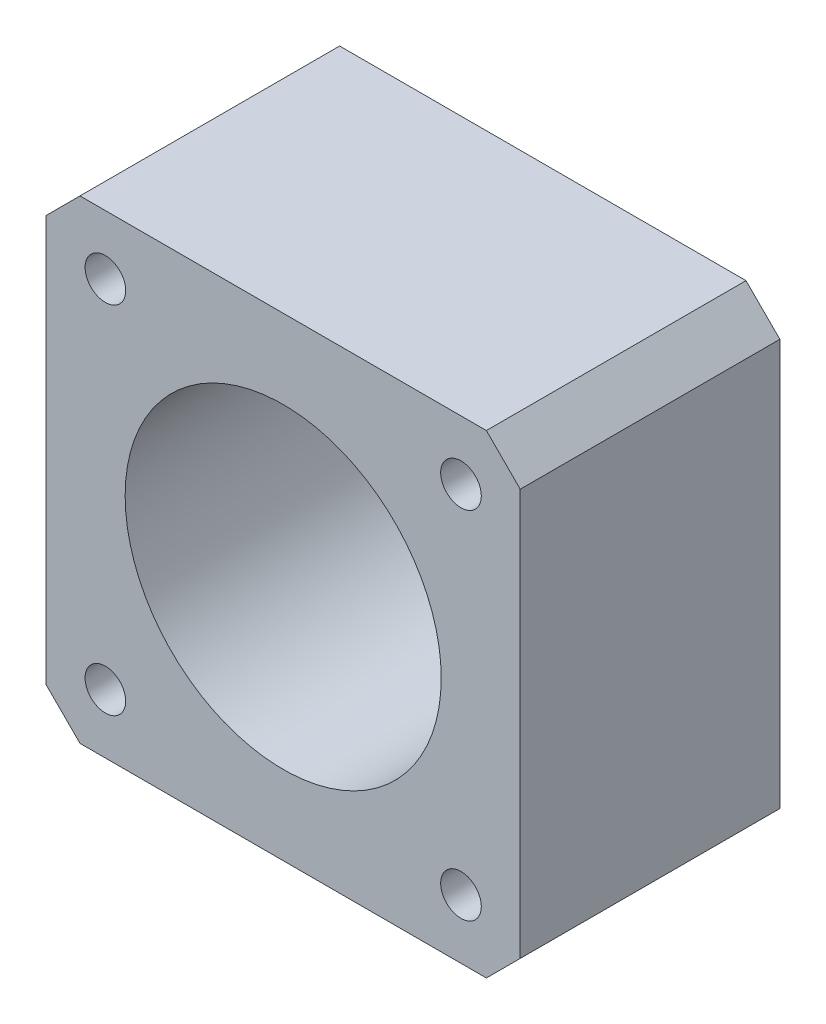
SolidWorks part; units mm, degrees
ref_plane "Front Plane" through (0, 0, 0) normal (0, 0, 1) x (1, 0, 0)
ref_plane "Top Plane" through (0, 0, 0) normal (0, 1, 0) x (1, 0, 0)
ref_plane "Right Plane" through (0, 0, 0) normal (1, 0, 0) x (0, 0, -1)
sketch "Sketch1" plane through (0, 0, 0) normal (0, 0, 1) x (1, 0, 0)
  line L1 (-21, 21) -> (21, 21)
  line L2 (-21, 21) -> (-21, -21)
  line L3 (-21, -21) -> (21, -21)
  line L4 (21, 21) -> (21, -21)
  line L5 (-21, 21) -> (21, -21) construction
  line L6 (-21, -21) -> (21, 21) construction
  point P0 (0, 0)
  dimension "D1" = 42
  dimension "D2" = 42
extrude "Boss-Extrude1" add sketch "Sketch1" along normal blind 23
sketch "Sketch2" plane through (0, 0, 23) normal (0, 0, 1) x (1, 0, 0)
  circle A0 centre (0, 0) radius 14
sketch "Sketch4" plane through (0, 0, 23) normal (0, 0, 1) x (1, 0, 0)
  line L1 (-15.75, -15.75) -> (15.75, -15.75) construction
  line L2 (-15.75, -15.75) -> (-15.75, 15.75) construction
  line L3 (-15.75, 15.75) -> (15.75, 15.75) construction
  line L4 (15.75, -15.75) -> (15.75, 15.75) construction
  line L5 (-15.75, -15.75) -> (15.75, 15.75) construction
  line L6 (-15.75, 15.75) -> (15.75, -15.75) construction
  circle A0 centre (-15.75, 15.75) radius 1.8
  circle A1 centre (15.75, 15.75) radius 1.8
  circle A2 centre (-15.75, -15.75) radius 1.8
  circle A3 centre (15.75, -15.75) radius 1.8
  point P0 (0, 0)
  dimension "D1" = 31.5
  dimension "D2" = 31.5
chamfer "Chamfer1" distance 3 angle 45 4 edges at (-21, -21, 11.5) (21, -21, 11.5) (21, 21, 11.5) (-21, 21, 11.5)
extrude "Вырез-Вытянуть2" cut sketch "Sketch4" against normal up to next
extrude "Вырез-Вытянуть3" cut sketch "Sketch2" against normal up to next
